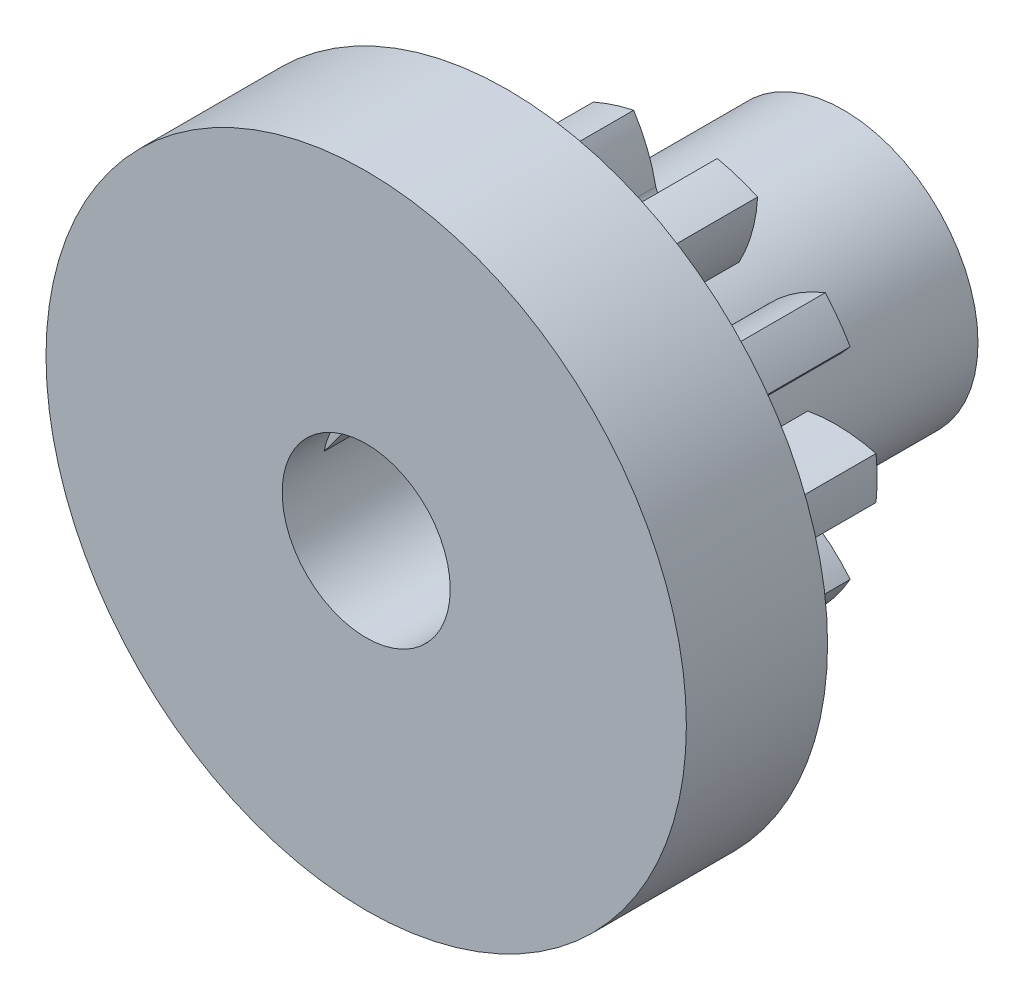
SolidWorks part; units mm, degrees
ref_plane "Front Plane" through (0, 0, 0) normal (0, 0, 1) x (1, 0, 0)
ref_plane "Top Plane" through (0, 0, 0) normal (0, 1, 0) x (1, 0, 0)
ref_plane "Right Plane" through (0, 0, 0) normal (1, 0, 0) x (0, 0, -1)
sketch "Sketch2" plane through (0, 0, 0) normal (0, 0, 1) x (1, 0, 0)
  circle A0 centre (0, 0) radius 10 construction
  circle A1 centre (0, 0) radius 12
  dimension "pitch cirlcle" = 20
  dimension "pitch circle 2" = 24
extrude "Boss-Extrude1" add sketch "Sketch2" along normal mid plane 20
sketch "Sketch3" plane through (0, 0, 10) normal (0, 0, 1) x (1, 0, 0)
  line L0 (0, 0) -> (0, 12) construction
  line L1 (7.0534, 9.7082) -> (0, 0) construction
  line L2 (0, 0) -> (3.7082, 11.4127) construction
  line L3 (0, 0) -> (-1.0821, 7.9265) construction
  line L4 (-1.5643, 9.8769) -> (1.5643, 9.8769) construction
  line L5 (1.5643, 9.8769) -> (4.5399, 8.9101) construction
  line L6 (0, 5.5789) -> (-2.259, 11.7855) construction
  arc A0 (1.0821, 7.9265) -> (-1.0821, 7.9265) centre (0, 0) ccw
  circle A2 centre (0, 0) radius 12 construction
  circle A3 centre (0, 0) radius 9.75 construction
  arc A4 (-2.486, 11.7397) -> (-1.0821, 7.9265) centre (-10.429, 6.6504) cw
  arc A5 (2.486, 11.7397) -> (1.0821, 7.9265) centre (10.429, 6.6504) ccw
  circle A6 centre (0, 0) radius 10 construction
  circle A7 centre (0, 0) radius 12 construction
  arc A8 (2.486, 11.7397) -> (-2.486, 11.7397) centre (0, 0) ccw
  dimension "angle displacement" = 36
  dimension "dedenum" = 4
  dimension "addendum" = 2.25
  dimension "Pressure Angle" = 20
extrude "Cut-Extrude1" cut sketch "Sketch3" against normal through all
fillet "Fillet1" radius 0.6 2 edges at (1.0821, 7.9265, 0) (-1.0821, 7.9265, 0)
sketch "Sketch4" plane through (0, 0, 10) normal (0, 0, 1) x (1, 0, 0)
  circle A0 centre (0, 0) radius 19.05
  dimension "D1" = 38.1
extrude "Boss-Extrude2" add sketch "Sketch4" along normal blind 8.4
pattern_circular "CirPattern1" count 10 over 360 about axis through (0, 0, 0) along (0, 0, 1) of "Cut-Extrude1"
sketch "Sketch5" plane through (0, 0, 18.4) normal (0, 0, 1) x (1, 0, 0)
  circle A0 centre (0, 0) radius 5
  dimension "D1" = 10
extrude "Cut-Extrude2" cut sketch "Sketch5" against normal blind 2.4
sketch "Sketch6" plane through (0, 0, 16) normal (0, 0, 1) x (1, 0, 0)
  line L0 (-4.9086, 0.9515) -> (-2.2968, 4.4412)
  arc A0 (-4.9086, 0.9515) -> (-2.2968, 4.4412) centre (0, 0) ccw
  circle A1 centre (0, 0) radius 5 construction
  dimension "D1" = 4.3589
extrude "Cut-Extrude3" cut sketch "Sketch6" against normal blind 20
sketch "Sketch7" plane through (0, 0, -10) normal (0, 0, -1) x (-1, 0, 0)
  circle A0 centre (0, 0) radius 8
  circle A1 centre (0, 0) radius 12
extrude "Cut-Extrude4" cut sketch "Sketch7" against normal blind 10
equation "\"module\"= 2mm"
equation "\"number of teeth\"= 10"
equation "\"pressure angle\"= 20"
equation "\"pitch cirlcle@Sketch2\"= \"module\" * \"number of teeth\""
equation "\"pitch circle 2@Sketch2\"= \"module\" * ( \"number of teeth\" + 2 )"
equation "\"angle displacement@Sketch3\"= 360 / \"number of teeth\""
equation "\"addendum@Sketch3\"= IIF ( \"module\" >= 1.25 , 2.25 , 2.4 )"
equation "\"Pressure Angle@Sketch3\"= \"pressure angle\""
equation "\"D1@CirPattern1\"=\"number of teeth\""
equation "\"D1@Fillet1\"= 0.3 * \"module\""
equation "\"dedenum@Sketch3\"= 2 * \"module\""
